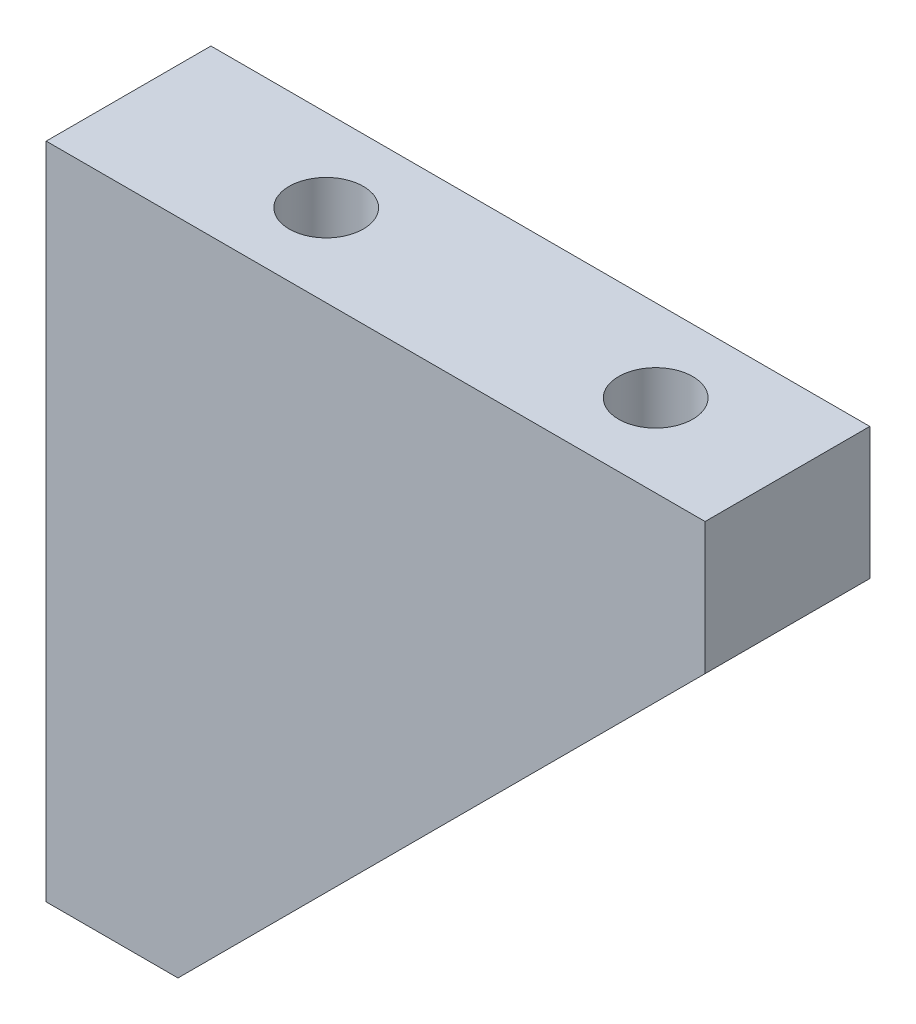
SolidWorks part; units mm, degrees
ref_plane "Alzado" through (0, 0, 0) normal (0, 0, 1) x (1, 0, 0)
ref_plane "Planta" through (0, 0, 0) normal (0, 1, 0) x (1, 0, 0)
ref_plane "Vista lateral" through (0, 0, 0) normal (1, 0, 0) x (0, 0, -1)
sketch "Croquis1" plane through (0, 0, 0) normal (0, 0, 1) x (1, 0, 0)
  line L0 (40, -8) -> (8, -40)
  line L1 (0, 0) -> (40, 0)
  line L2 (0, 0) -> (0, -40)
  line L3 (0, -40) -> (8, -40)
  line L4 (40, 0) -> (40, -8)
  dimension "D1" = 40
  dimension "D2" = 40
  dimension "D3" = 8
  dimension "D4" = 8
extrude "Saliente-Extruir1" add sketch "Croquis1" along normal blind 10
hole_wizard "Taladro de margen para M41" positions "Croquis2" profile "Croquis3" hole size "M4" standard "DIN"
sketch "Croquis2" plane through (0, 0, 0) normal (0, 1, 0) x (1, 0, 0)
  line L0 (0, -5) -> (40, -5) construction
  line L1 (0, -10) -> (0, 0) construction
  line L2 (40, -10) -> (40, 0) construction
  point P0 (12, -5)
  point P2 (32, -5)
  point P13 (10.9334, -5)
  point P14 (26.8163, -5)
  dimension "D1" = 12
  dimension "D2" = 8
sketch "Croquis3" plane through (12, 0, 5) normal (1, 0, 0) x (0, 0, 1)
  line L0 (0, 0) -> (0, 11.3519)
  line L1 (0, 11.3519) -> (2.25, 10)
  line L2 (2.25, 10) -> (2.25, 0)
  line L5 (2.25, 0) -> (0, 0)
  line L10 (0, 11.3519) -> (-2.25, 10) construction
  line L11 (0, -6.35) -> (0, 107.95) construction
  dimension "Diámetro de taladro" = 4.5
  dimension "Profundidad de taladro" = 10
  dimension "Ángulo de perforador" = 118
hole_wizard "Taladro de margen para M42" positions "Croquis6" profile "Croquis5" hole size "M4" standard "DIN"
sketch "Croquis6" plane through (0, 0, 0) normal (-1, 0, 0) x (0, 0, 1)
  line L0 (5, -40) -> (5, 0) construction
  line L1 (10, -40) -> (0, -40) construction
  line L2 (10, 0) -> (0, 0) construction
  point P0 (5, -12)
  point P2 (5, -32)
  point P13 (5, -29.8191)
  point P14 (5, -8.9804)
  point P15 (0, 0)
  dimension "D1" = 8
  dimension "D2" = 12
sketch "Croquis5" plane through (0, -12, 5) normal (0, 1, 0) x (0, 0, 1)
  line L0 (0, 0) -> (0, 11.3519)
  line L1 (0, 11.3519) -> (2.25, 10)
  line L2 (2.25, 10) -> (2.25, 0)
  line L5 (2.25, 0) -> (0, 0)
  line L10 (0, 11.3519) -> (-2.25, 10) construction
  line L11 (0, -6.35) -> (0, 107.95) construction
  dimension "Diámetro de taladro" = 4.5
  dimension "Profundidad de taladro" = 10
  dimension "Ángulo de perforador" = 118
